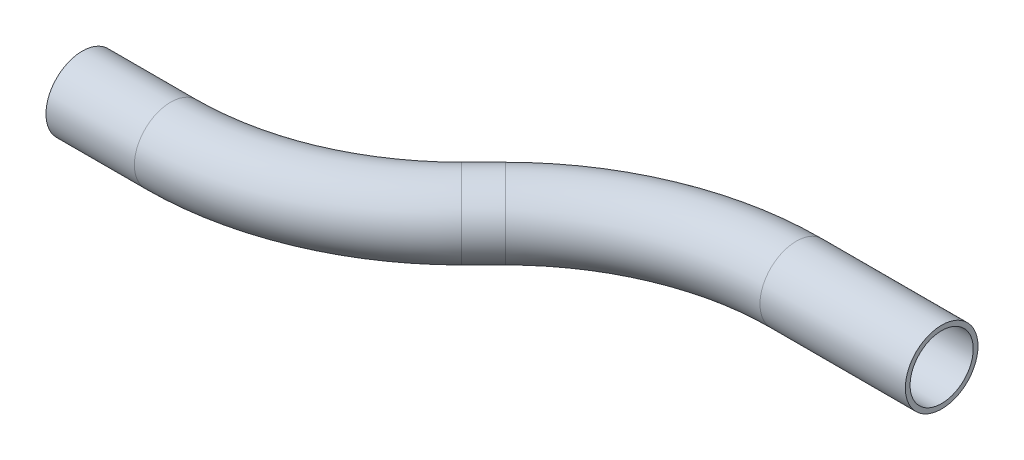
SolidWorks part; units mm, degrees
ref_plane "Front Plane" through (0, 0, 0) normal (0, 0, 1) x (1, 0, 0)
ref_plane "Top Plane" through (0, 0, 0) normal (0, 1, 0) x (1, 0, 0)
ref_plane "Right Plane" through (0, 0, 0) normal (1, 0, 0) x (0, 0, -1)
sketch "Sketch1" plane through (0, 0, 0) normal (0, 1, 0) x (1, 0, 0)
  line L0 (0, 0) -> (23.1756, 0)
  line L1 (77.0571, 22.3185) -> (82.8363, 28.0977)
  line L2 (136.7179, 50.4161) -> (174.8179, 50.4161)
  arc A1 (82.8363, 28.0977) -> (136.7179, 50.4161) centre (136.7179, -25.7839) cw
  arc A2 (23.1756, 0) -> (77.0571, 22.3185) centre (23.1756, 76.2) ccw
  point P10 (105.1548, 50.4161)
  point P14 (54.7387, 0)
  dimension "D3" = 76.2
  dimension "D1" = 54.7387
  dimension "D2" = 38.1
  dimension "D4" = 45
  dimension "D5" = 50.4161
ref_plane "Plane1" through (0, 0, 0) normal (1, 0, 0) x (0, 0, -1)
sketch "Sketch2" plane through (0, 0, 0) normal (1, 0, 0) x (0, 0, -1)
  circle A0 centre (0, 0) radius 9.525
  circle A1 centre (0, 0) radius 8.2804
  dimension "D1" = 19.05
  dimension "D2" = 1.2446
sweep "Sweep1" add profiles "Sketch2" path "Sketch1"
